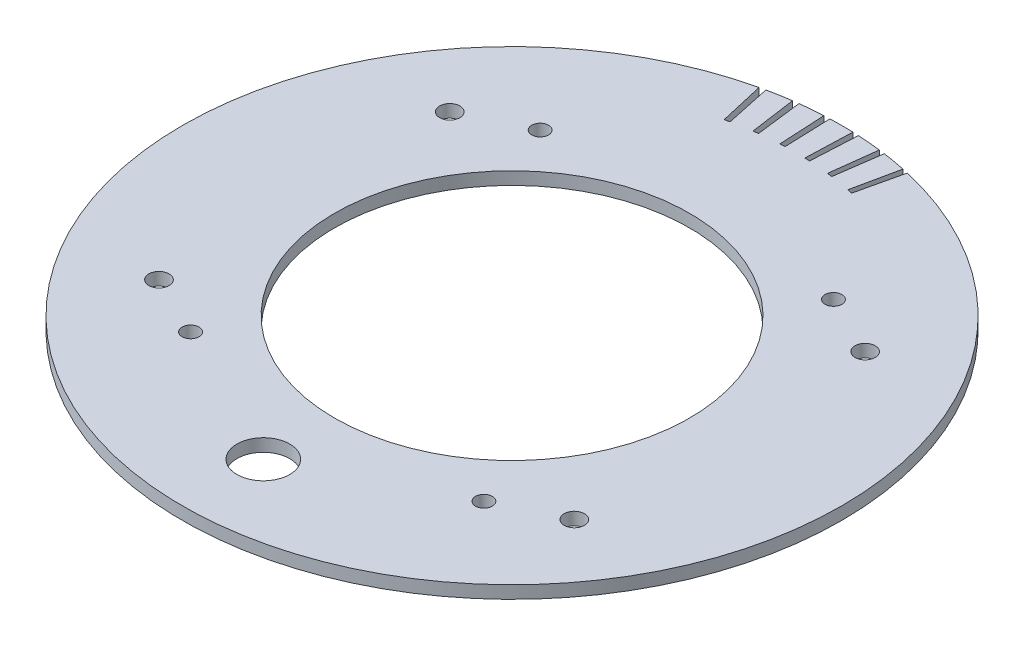
SolidWorks part; units mm, degrees
material "G10 Fiber Reinforced Plastic"
ref_plane "Front Plane" through (0, 0, 0) normal (0, 0, 1) x (1, 0, 0)
ref_plane "Top Plane" through (0, 0, 0) normal (0, 1, 0) x (1, 0, 0)
ref_plane "Right Plane" through (0, 0, 0) normal (1, 0, 0) x (0, 0, -1)
sketch "98mm - 6ID centering ring sketch" plane through (0, 0, 0) normal (0, 1, 0) x (1, 0, 0)
  line L0 (0, 0) -> (0, 50000) construction
  line L1 (0, 0) -> (50000, 0) construction
  line L2 (99.0091, 3.175) -> (56.4257, 3.175)
  line L3 (-99.0091, -3.175) -> (-56.4257, -3.175)
  line L4 (3.175, -99.0091) -> (3.175, -56.4257)
  line L5 (-3.175, 99.0091) -> (-3.175, 56.4257)
  line L7 (-56.4257, 3.175) -> (-99.0091, 3.175)
  line L8 (-3.175, -56.4257) -> (-3.175, -99.0091)
  line L9 (3.175, 56.4257) -> (3.175, 99.0091)
  line L11 (56.4257, -3.175) -> (99.0091, -3.175)
  circle A0 centre (0, 0) radius 99.06
  circle A1 centre (0, 0) radius 53.34
  arc A2 (-56.4257, 3.175) -> (-56.4257, -3.175) centre (0, 0) ccw
  arc A3 (-3.175, -56.4257) -> (3.175, -56.4257) centre (0, 0) ccw
  arc A4 (56.4257, -3.175) -> (56.4257, 3.175) centre (0, 0) ccw
  arc A5 (3.175, 56.4257) -> (-3.175, 56.4257) centre (0, 0) ccw
  dimension "D1" = 45.72
  dimension "D2" = 106.68
  dimension "D5" = 3.175
  dimension "D3" = 6.35
  dimension "D4" = 6.35
  dimension "D6" = 6.35
extrude "Centering Ring Extrude" add sketch "98mm - 6ID centering ring sketch" along normal blind 1.905 and the other way blind 1.905 contours L9 A5 L5 A0 L7 A2 L3 L8 A3 L4 L11 A4 L2 A1 | A4 L11 A0 L2 | A5 L9 A0 L5 | A2 L7 A0 L3 | A3 L8 A0 L4
sketch "Sketch1" plane through (0, -1.905, 0) normal (0, -1, 0) x (1, 0, 0)
  line L0 (0, 0) -> (14.5226, 68.3236) construction
  line L1 (0, 0) -> (32.7926, -61.6739)
  line L2 (0, 0) -> (-55.0426, -43.004)
  line L3 (0, 0) -> (0, 69.85) construction
  circle A0 centre (0, 0) radius 69.85 construction
  circle A1 centre (32.7926, -61.6739) radius 3.175
  circle A2 centre (-55.0426, -43.004) radius 3.175
  dimension "D1" = 139.7
  dimension "D2" = 6.35
  dimension "D3" = 140
  dimension "D4" = 12
sketch "Sketch3" plane through (0, 1.905, 0) normal (0, 1, 0) x (1, 0, 0)
  line L0 (0, 0) -> (0, 99.06) construction
  line L1 (0, 0) -> (-22.2837, 96.5211)
  line L2 (0, 0) -> (-20.5957, 96.8953)
  circle A0 centre (0, 0) radius 99.06 construction
  circle A1 centre (0, 0) radius 99.06
  circle A2 centre (0, 0) radius 85.09
  circle M8 centre (0, 0) radius 99.06
  dimension "D1" = 13.97
  dimension "D2" = 12
  dimension "D3" = 1
extrude "Cut-Extrude3" cut sketch "Sketch3" against normal through all contours A2 L2 L1 M8
pattern_circular "CirPattern1" count 6 every 5 about axis through (0, 0, 0) along (0, 1, 0) of "Cut-Extrude3"
sketch "Sketch4" plane through (0, 1.905, 0) normal (0, 1, 0) x (1, 0, 0)
  line L0 (0, 0) -> (76.2, 0) construction
  line L1 (69.0607, 32.2035) -> (0, 0) construction
  line L2 (-75.0424, 13.232) -> (0, 0) construction
  line L3 (-58.3726, -48.9804) -> (0, 0) construction
  line L4 (0, 0) -> (65.9911, -38.1) construction
  circle A0 centre (0, 0) radius 76.2 construction
  circle A1 centre (69.0607, 32.2035) radius 3
  circle A2 centre (-75.0424, 13.232) radius 3
  circle A3 centre (65.9911, -38.1) radius 3
  circle A4 centre (-58.3726, -48.9804) radius 3
  dimension "D1" = 152.4
  dimension "D2" = 6
  dimension "D3" = 335
  dimension "D4" = 190
  dimension "D5" = 330
  dimension "D6" = 140
sketch "Sketch5" plane through (0, -1.905, 0) normal (0, -1, 0) x (1, 0, 0)
  line L0 (0, 0) -> (0, -99.06) construction
  line L1 (0, 0) -> (99.06, 0) construction
  line L2 (44.0824, 52.5353) -> (-44.0824, 52.5353) construction
  line L3 (-44.0824, 52.5353) -> (-44.0824, -52.5353) construction
  line L4 (-44.0824, -52.5353) -> (44.0824, -52.5353) construction
  line L5 (44.0824, -52.5353) -> (44.0824, 52.5353) construction
  line L6 (62.4194, 43.7065) -> (-62.4194, 43.7065) construction
  line L7 (-62.4194, 43.7065) -> (-62.4194, -43.7065) construction
  line L8 (-62.4194, -43.7065) -> (62.4194, -43.7065) construction
  line L9 (62.4194, -43.7065) -> (62.4194, 43.7065) construction
  line L10 (-44.0824, 52.5353) -> (44.0824, -52.5353) construction
  line L11 (44.0824, 52.5353) -> (-44.0824, -52.5353) construction
  line L12 (-62.4194, 43.7065) -> (62.4194, -43.7065) construction
  line L13 (62.4194, 43.7065) -> (-62.4194, -43.7065) construction
  line L14 (0, 74.7547) -> (0, 0) construction
  arc A0 (-3.4571, -98.9997) -> (3.4571, -98.9997) centre (0, 0) ccw construction
  circle A1 centre (-62.4194, 43.7065) radius 3.048
  circle A2 centre (-44.0824, 52.5353) radius 2.54
  circle A3 centre (44.0824, 52.5353) radius 2.54
  circle A4 centre (62.4194, 43.7065) radius 3.048
  circle A5 centre (62.4194, -43.7065) radius 3.048
  circle A6 centre (44.0824, -52.5353) radius 2.54
  circle A7 centre (-44.0824, -52.5353) radius 2.54
  circle A8 centre (-62.4194, -43.7065) radius 3.048
  arc A9 (22.2837, -96.5211) -> (-22.2837, -96.5211) centre (0, 0) ccw construction
  circle A10 centre (0, 74.7547) radius 7.9375
  point P24 (0, 0)
  point P25 (0, 0)
  dimension "D2" = 5.08
  dimension "D3" = 5.08
  dimension "D4" = 5.08
  dimension "D5" = 5.08
  dimension "D6" = 6.096
  dimension "D7" = 6.096
  dimension "D8" = 6.096
  dimension "D9" = 6.096
  dimension "D16" = 15.875
  dimension "D10" = 88.1647
  dimension "D11" = 105.0707
  dimension "D12" = 124.8388
  dimension "D13" = 87.413
  dimension "D14" = 90
  dimension "D15" = 74.7547
extrude "Cut-Extrude4" cut sketch "Sketch5" against normal up to surface (3.81 mm away) up to face at (0, 1.905, 53.34)
